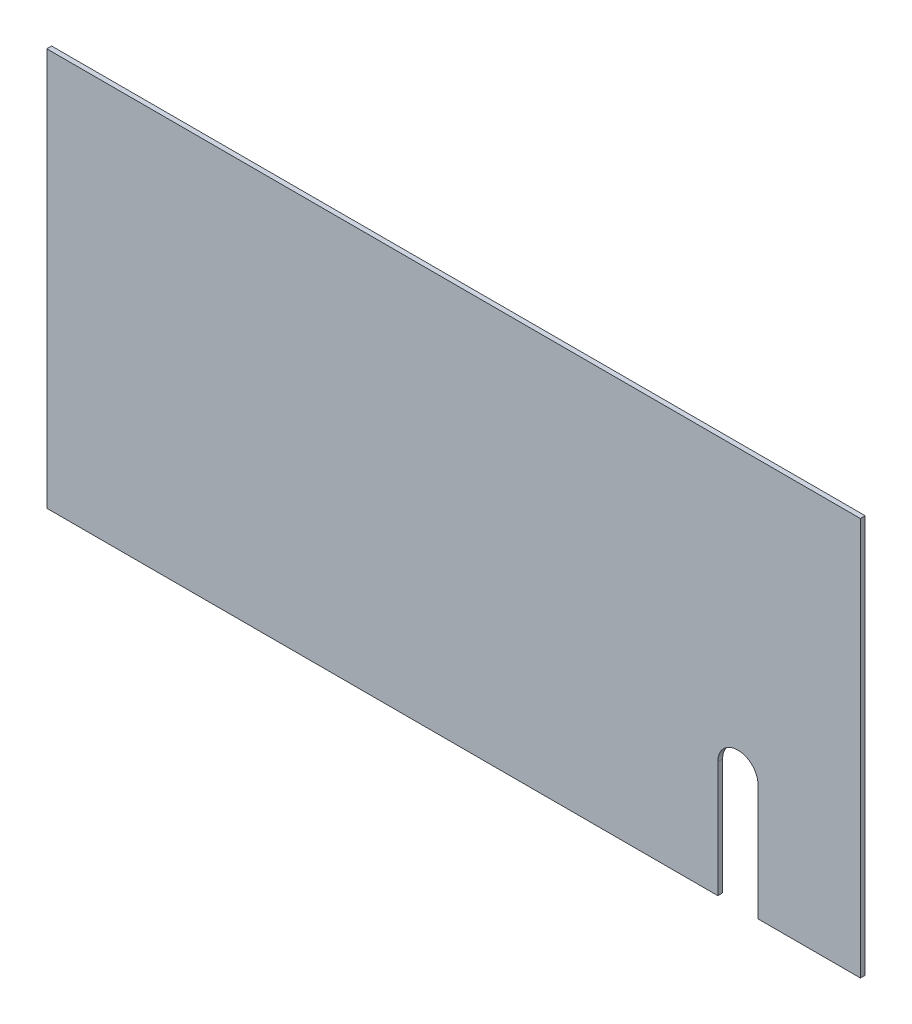
SolidWorks part; units mm, degrees
ref_plane "Plan de face" through (0, 0, 0) normal (0, 0, 1) x (1, 0, 0)
ref_plane "Plan de dessus" through (0, 0, 0) normal (0, 1, 0) x (1, 0, 0)
ref_plane "Plan de droite" through (0, 0, 0) normal (1, 0, 0) x (0, 0, -1)
sketch "Esquisse1" plane through (0, 0, 0) normal (0, 0, 1) x (1, 0, 0)
  line L1 (230.5, -2.1662) -> (-274.5, -2.1662)
  line L2 (230.5, -2.1662) -> (230.5, 244.8338)
  line L3 (230.5, 244.8338) -> (-274.5, 244.8338)
  line L4 (-274.5, -2.1662) -> (-274.5, 244.8338)
  dimension "D1" = 505
extrude "Boss.-Extru.1" add sketch "Esquisse1" along normal blind 3
sketch "Esquisse3" plane through (0, 0, 3) normal (0, 0, 1) x (1, 0, 0)
  line L0 (-274.5, -2.1662) -> (230.5, -2.1662) construction
  line L1 (-169.5, 183.8338) -> (30.5, 183.8338) construction
  line L2 (-169.5, 183.8338) -> (-169.5, 87.8338) construction
  line L3 (-169.5, 87.8338) -> (30.5, 87.8338) construction
  line L4 (30.5, 183.8338) -> (30.5, 87.8338) construction
  line L5 (-274.5, -2.1662) -> (230.5, -2.1662) construction
  line L6 (230.5, -2.1662) -> (230.5, 244.8338) construction
  line L7 (142, 69.8338) -> (142, -28.1662)
  line L8 (167, 69.8338) -> (167, -28.1662)
  line L9 (230.5, -2.1662) -> (230.5, 244.8338) construction
  line L10 (167, -28.1662) -> (142, -28.1662)
  circle A0 centre (-169.5, 183.8338) radius 6.5 construction
  circle A1 centre (-169.5, 87.8338) radius 6.5 construction
  circle A2 centre (30.5, 87.8338) radius 6.5 construction
  circle A3 centre (30.5, 183.8338) radius 6.5 construction
  arc A4 (167, 69.8338) -> (142, 69.8338) centre (154.5, 69.8338) ccw
  dimension "D1" = 13
  dimension "D6" = 25
  dimension "D7" = 72
  dimension "D8" = 76
  dimension "D2" = 96
  dimension "D3" = 200
  dimension "D4" = 90
  dimension "D5" = 200
extrude "Enlèv. mat.-Extru.2" cut sketch "Esquisse3" against normal blind 72
sketch "Esquisse5" plane through (0, 0, 3) normal (0, 0, 1) x (1, 0, 0)
  arc A0 (191.1507, 88.1102) -> (117.0302, 53.3017) centre (154.5, 69.8338) ccw construction
  text T0 "Direction" font "Century Gothic" height in points 72
  point P0 (117.0302, 53.3017)
  point P4 (108.0022, 110.6937)
  point P6 (195.0576, 90.0584)
  point P7 (95.1052, 53.3017)
  point P8 (154.5, 73.937)
